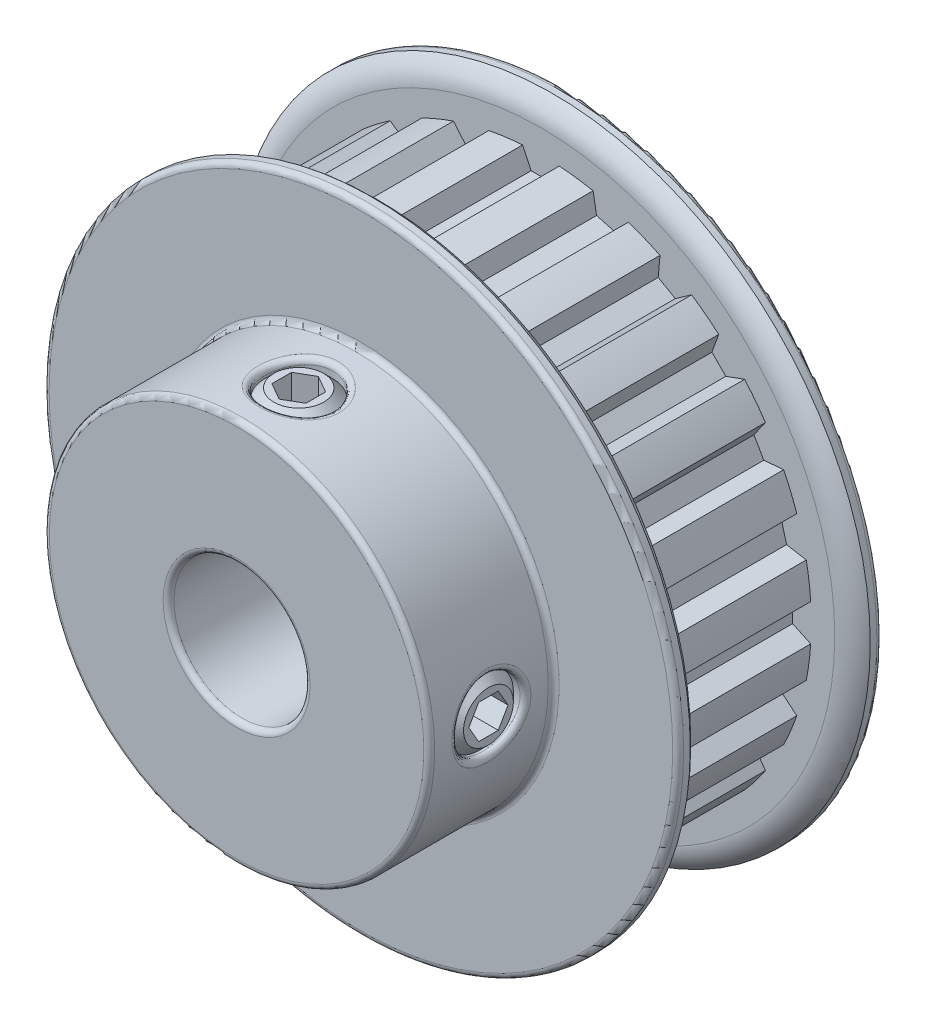
SolidWorks part; units mm, degrees
ref_plane "Front Plane" through (0, 0, 0) normal (0, 0, 1) x (1, 0, 0)
ref_plane "Top Plane" through (0, 0, 0) normal (0, 1, 0) x (1, 0, 0)
ref_plane "Right Plane" through (0, 0, 0) normal (1, 0, 0) x (0, 0, -1)
sketch "Sketch1" plane through (0, 0, 0) normal (0, 0, 1) x (1, 0, 0)
  line L0 (-1.2827, 18.8976) -> (-0.6905, 17.6276)
  line L1 (-0.6905, 17.6276) -> (0.6905, 17.6276)
  line L2 (0.6905, 17.6276) -> (1.2827, 18.8976)
  line L3 (-1.2827, 18.8976) -> (1.2827, 18.8976)
  line L4 (0, 0) -> (0, 17.6276) construction
  line L5 (0, 17.6276) -> (0, 19.9136) construction
  circle A0 centre (0, 0) radius 19.4056 construction
  circle A1 centre (0, 0) radius 22.225 construction
  circle A2 centre (0, 0) radius 18.9411 construction
  point P6 (0, 18.8976)
  point P11 (0, 19.4056)
  point P13 (0, 22.225)
  point P14 (0, 18.9411)
  dimension "D1" = 1.016
  dimension "D2" = 0.508
sketch "Sketch2" plane through (0, 0, 0) normal (1, 0, 0) x (0, 0, -1)
  line L0 (-11.5062, 4.7625) -> (11.5062, 4.7625)
  line L1 (-11.5062, 4.7625) -> (-11.5062, 13.5001)
  line L2 (-11.5062, 13.5001) -> (-2.794, 13.5001)
  line L3 (-2.794, 13.5001) -> (-2.794, 22.225)
  line L4 (-2.794, 22.225) -> (-1.1049, 22.225) construction
  line L5 (-1.1049, 22.225) -> (-1.1049, 18.9411) construction
  line L6 (-1.1049, 18.9411) -> (9.8171, 18.9411)
  line L7 (9.8171, 18.9411) -> (9.8171, 22.225) construction
  line L8 (9.8171, 22.225) -> (11.5062, 22.225) construction
  line L9 (11.5062, 22.225) -> (11.5062, 4.7625)
  line L10 (-11.5062, 0) -> (11.5062, 0) construction
  line L13 (-2.794, 22.225) -> (-1.9494, 22.225)
  line L14 (-1.1049, 20.583) -> (-1.1049, 18.9411)
  line L15 (9.8171, 18.9411) -> (9.8171, 20.583)
  line L16 (10.6617, 22.225) -> (11.5062, 22.225)
  arc A0 (-1.1049, 20.583) -> (-1.9494, 22.225) centre (-3.1233, 20.583) ccw
  arc A1 (9.8171, 20.583) -> (10.6617, 22.225) centre (11.8355, 20.583) cw
  point P12 (-1.1049, 20.583)
  point P14 (-1.9494, 22.225)
  point P20 (9.8171, 20.583)
  point P21 (10.6617, 22.225)
  point P25 (9.8171, 0)
  point P26 (-1.1049, 0)
  dimension "Bore" = 9.525
  dimension "Hub Dia" = 27.0002
  dimension "Outside Width" = 14.3002
  dimension "Inside Width" = 10.922
revolve "Revolve1" add sketch "Sketch2" angle 360 mid plane about L10
sketch "Sketch3" plane through (0, 0, 0) normal (0, 0, 1) x (1, 0, 0)
  line L0 (-0.6905, 17.6276) -> (0.6905, 17.6276) construction
  line L1 (0.6905, 17.6276) -> (1.2827, 18.8976) construction
  line L2 (-1.2827, 18.8976) -> (-0.6905, 17.6276) construction
  line L3 (-0.6905, 17.6276) -> (0.6905, 17.6276)
  line L4 (0.6905, 17.6276) -> (1.2827, 18.8976)
  line L5 (-1.2827, 18.8976) -> (-0.6905, 17.6276)
  circle A0 centre (0, 0) radius 18.9411 construction
  arc A1 (1.2827, 18.8976) -> (-1.2827, 18.8976) centre (0, 0) ccw
extrude "Cut-Extrude1" cut sketch "Sketch3" against normal up to vertex (9.8171 mm away) from vertex at 1.1049 starting at point (0, 18.9411, 1.1049)
pattern_circular "CirPattern1" count 24 over 360 about axis through (0, 0, 0) along (0, 0, 1) of "Cut-Extrude1"
sketch "Sketch4" plane through (0, 0, 0) normal (0, 1, 0) x (1, 0, 0)
  line L0 (0, -2.794) -> (0, -11.5062) construction
  line L1 (-13.5001, -2.794) -> (13.5001, -2.794) construction
  line L2 (-13.5001, -11.5062) -> (13.5001, -11.5062) construction
  circle A0 centre (0, -7.1501) radius 2.3813
  dimension "D1" = 4.7625
extrude "Cut-Extrude2" cut sketch "Sketch4" along normal through all
ref_plane "Plane1" through (0, 0, 7.1501) normal (0, 0, 1) x (1, 0, 0)
sketch "Sketch5" plane through (0, 0, 7.1501) normal (0, 0, 1) x (1, 0, 0)
  line L0 (0, 0) -> (0, 13.5001) construction
  line L1 (-2.3812, 13.2884) -> (-2.3812, 4.1244) construction
  line L2 (-2.3812, 13.2884) -> (-2.3812, 4.1244) construction
  line L3 (0, 13.2884) -> (0, 4.7625)
  line L4 (0, 4.7625) -> (-1.7462, 4.7625)
  line L5 (-2.3812, 12.6534) -> (-2.3812, 5.3975)
  line L6 (-1.7462, 13.2884) -> (0, 13.2884)
  line L7 (-2.3812, 12.6534) -> (-1.7462, 13.2884)
  line L8 (-2.3812, 5.3975) -> (-1.7462, 4.7625)
  circle A0 centre (0, 0) radius 13.5001 construction
  circle A3 centre (0, 0) radius 4.7625 construction
  point P13 (-2.3812, 4.7625)
  point P15 (-2.3812, 13.2884)
revolve "Revolve2" add sketch "Sketch5" angle 360 mid plane about L0
sketch "Sketch6" plane through (0, 13.2884, 0) normal (0, -1, 0) x (-1, 0, 0)
  line L1 (0, -5.7753) -> (-1.1906, -6.4627)
  line L2 (-1.1906, -6.4627) -> (-1.1906, -7.8375)
  line L3 (-1.1906, -7.8375) -> (0, -8.5249)
  line L4 (0, -8.5249) -> (1.1906, -7.8375)
  line L5 (1.1906, -7.8375) -> (1.1906, -6.4627)
  line L6 (1.1906, -6.4627) -> (0, -5.7753)
  circle A0 centre (0, -7.1501) radius 1.1906 construction
  dimension "D1" = 2.3813
extrude "Cut-Extrude3" cut sketch "Sketch6" along normal blind 1.7859
pattern_circular "CirPattern2" count 2 every 90 about axis through (0, 0, 0) along (0, 0, 1) of "Cut-Extrude2", "Revolve2", "Cut-Extrude3"
fillet "Fillet1" radius 0.381 8 edges at (13.4906, -0.5064, 9.4769) (0.5064, 13.4906, 9.4769) (13.5001, 0, 11.5062) (4.7625, 0, 11.5062) (22.225, 0, 2.794) (13.5001, 0, 2.794) (4.7625, 0, -11.5062) (22.225, 0, -11.5062)
equation "\"D2@Sketch1\" = \"D1@Sketch1\"/2"
equation "\"D1@Sketch4\" = \"Bore@Sketch2\"/2"
equation "\"D1@Sketch6\" = \"D1@Sketch4\"/2"
equation "\"D1@Cut-Extrude3\" = \"D1@Sketch6\"*.75"
